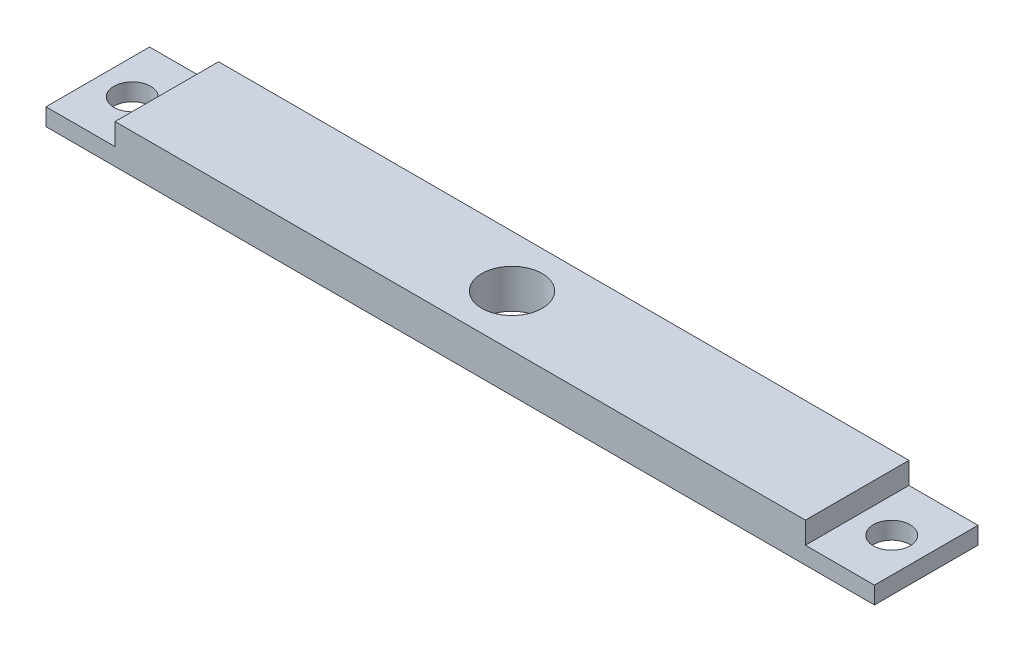
SolidWorks part; units mm, degrees
material "ABS PC"
ref_plane "Front Plane" through (0, 0, 0) normal (0, 0, 1) x (1, 0, 0)
ref_plane "Top Plane" through (0, 0, 0) normal (0, 1, 0) x (1, 0, 0)
ref_plane "Right Plane" through (0, 0, 0) normal (1, 0, 0) x (0, 0, -1)
sketch "Sketch1" plane through (0, 0, 0) normal (0, 0, 1) x (1, 0, 0)
  line L0 (-76.2, 0) -> (76.2, 0)
  line L1 (76.2, 0) -> (76.2, 3.175)
  line L2 (76.2, 3.175) -> (63.5, 3.175)
  line L3 (63.5, 3.175) -> (63.5, 7.1755)
  line L4 (63.5, 7.1755) -> (-63.5, 7.1755)
  line L5 (-63.5, 7.1755) -> (-63.5, 3.175)
  line L6 (-63.5, 3.175) -> (-76.2, 3.175)
  line L7 (-76.2, 3.175) -> (-76.2, 0)
  point P4 (0, 0)
  dimension "D1" = 152.4
  dimension "D2" = 12.7
  dimension "D3" = 12.7
  dimension "D4" = 7.1755
  dimension "D5" = 3.175
  dimension "D6" = 3.175
extrude "Boss-Extrude1" add sketch "Sketch1" along normal blind 19.05
sketch "Sketch2" plane through (0, 7.1755, 0) normal (0, 1, 0) x (1, 0, 0)
  line L0 (63.5, 0) -> (-63.5, 0) construction
  line L1 (-76.2, -19.05) -> (-76.2, 0) construction
  circle A0 centre (0, -9.525) radius 5.5562
  dimension "D1" = 11.1125
  dimension "D2" = 9.525
  dimension "D3" = 76.2
extrude "Cut-Extrude1" cut sketch "Sketch2" against normal through all
sketch "Sketch3" plane through (0, 3.175, 0) normal (0, 1, 0) x (1, 0, 0)
  line L0 (0, 3.842) -> (0, -3.842) construction
  line L1 (-63.5, 0) -> (-76.2, 0) construction
  line L2 (76.2, 0) -> (63.5, 0) construction
  line L4 (-76.2, -19.05) -> (-76.2, 0) construction
  line L5 (76.2, -19.05) -> (76.2, 0) construction
  circle A0 centre (-69.85, -9.525) radius 3.3782
  circle A1 centre (69.85, -9.525) radius 3.3782
  point P2 (0, 0)
  dimension "D1" = 6.7564
  dimension "D2" = 6.7564
  dimension "D3" = 9.525
  dimension "D4" = 9.525
  dimension "D5" = 6.35
  dimension "D6" = 6.35
extrude "Cut-Extrude2" cut sketch "Sketch3" against normal through all
